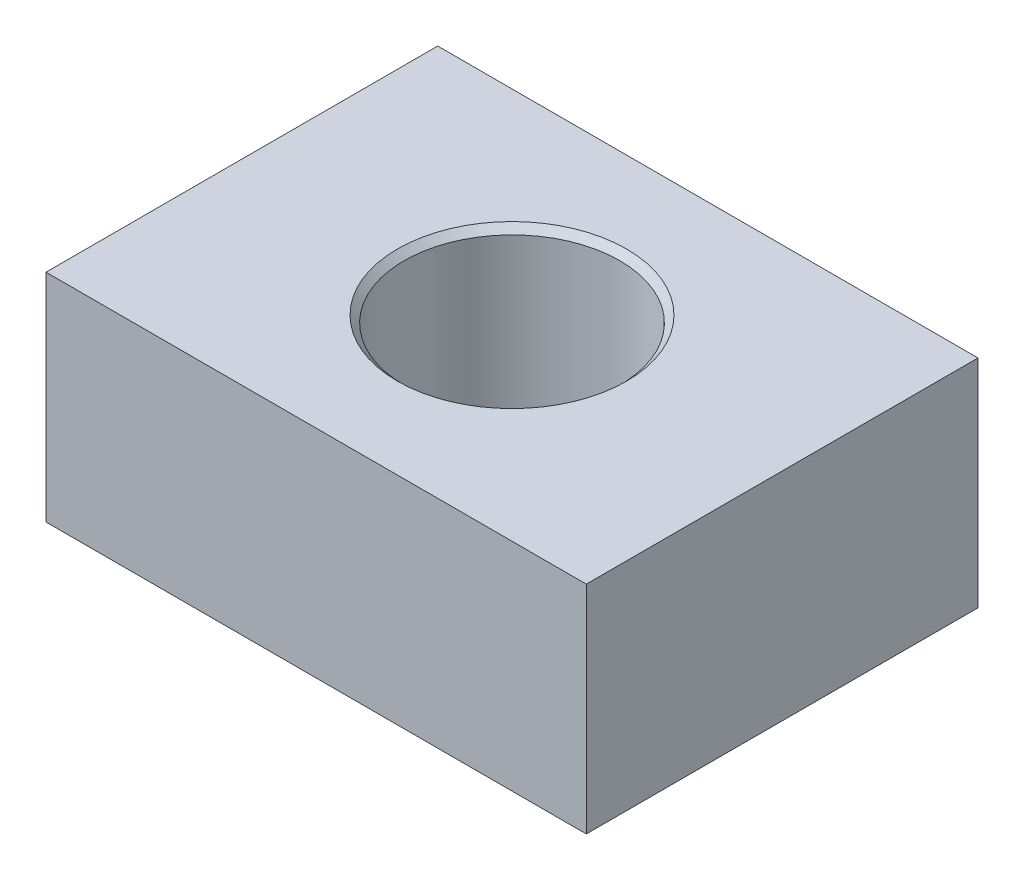
SolidWorks part; units mm, degrees
ref_plane "Front Plane" through (0, 0, 0) normal (0, 0, 1) x (1, 0, 0)
ref_plane "Top Plane" through (0, 0, 0) normal (0, 1, 0) x (1, 0, 0)
ref_plane "Right Plane" through (0, 0, 0) normal (1, 0, 0) x (0, 0, -1)
sketch "Sketch1" plane through (0, 0, 0) normal (0, 1, 0) x (1, 0, 0)
  line L1 (-10, -7.25) -> (10, -7.25)
  line L2 (-10, -7.25) -> (-10, 7.25)
  line L3 (-10, 7.25) -> (10, 7.25)
  line L4 (10, -7.25) -> (10, 7.25)
  line L5 (-10, -7.25) -> (10, 7.25) construction
  line L6 (-10, 7.25) -> (10, -7.25) construction
  circle A0 centre (0, 0) radius 3.99
  point P0 (0, 0)
  dimension "D3" = 7.98
  dimension "D1" = 14.5
  dimension "D2" = 20
extrude "Extrude1" add sketch "Sketch1" along normal blind 8.01
chamfer "Chamfer1" distance 0.25 angle 45 2 edges at (0, 8.01, 3.99) (0, 0, 3.99)
